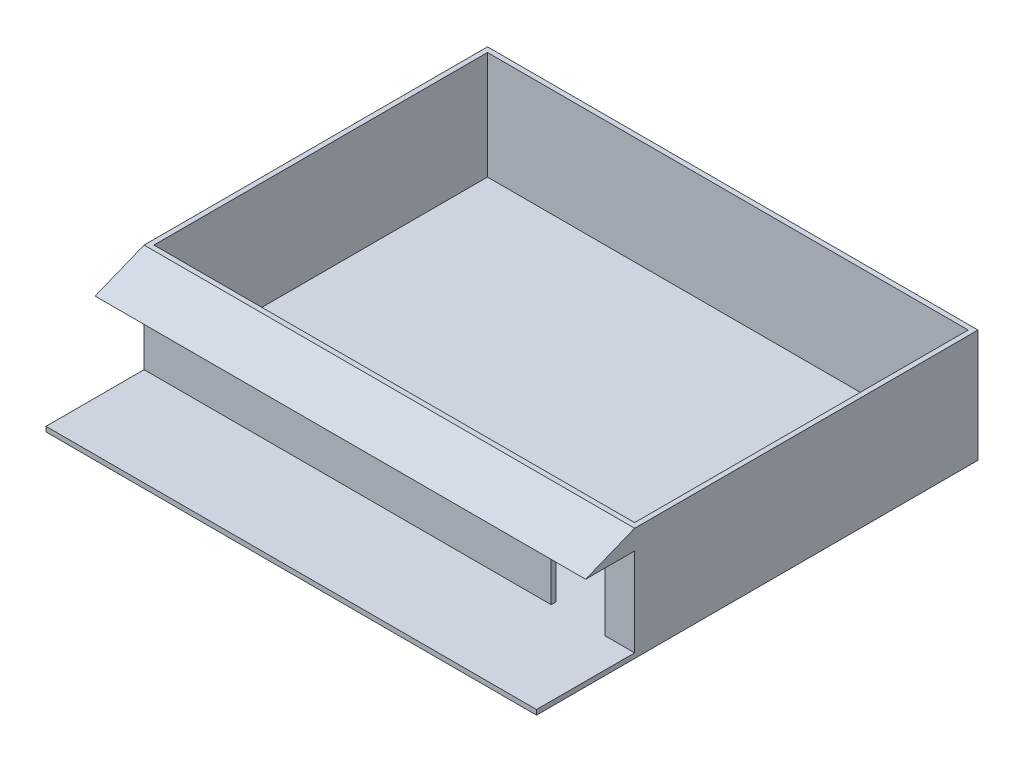
SolidWorks part; units mm, degrees
ref_plane "Front Plane" through (0, 0, 0) normal (0, 0, 1) x (1, 0, 0)
ref_plane "Top Plane" through (0, 0, 0) normal (0, 1, 0) x (1, 0, 0)
ref_plane "Right Plane" through (0, 0, 0) normal (1, 0, 0) x (0, 0, -1)
sketch "Sketch1" plane through (0, 0, 0) normal (0, 1, 0) x (1, 0, 0)
  line L1 (-500, 450) -> (500, 450)
  line L2 (-500, 450) -> (-500, -450)
  line L3 (-500, -450) -> (500, -450)
  line L4 (500, 450) -> (500, -450)
  line L5 (-500, 450) -> (500, -450) construction
  line L6 (-500, -450) -> (500, 450) construction
  point P0 (0, 0)
  dimension "D1" = 1000
  dimension "D2" = 900
extrude "Boss-Extrude1" add sketch "Sketch1" along normal blind 10
sketch "Sketch2" plane through (0, 10, 0) normal (0, 1, 0) x (1, 0, 0)
  line L1 (-500, -250) -> (500, -250)
  line L2 (-500, -250) -> (-500, 450)
  line L3 (-500, 450) -> (500, 450)
  line L4 (500, -250) -> (500, 450)
  line L5 (-500, -250) -> (500, 450) construction
  line L6 (-500, 450) -> (500, -250) construction
  line L7 (-490, -240) -> (490, -240)
  line L8 (-490, -240) -> (-490, 440)
  line L9 (-490, 440) -> (490, 440)
  line L10 (490, -240) -> (490, 440)
  line L11 (-490, -240) -> (490, 440) construction
  line L12 (-490, 440) -> (490, -240) construction
  point P0 (0, 64.0641)
  point P7 (0, 100)
  dimension "D1" = 980
  dimension "D2" = 680
  dimension "D3" = 10
extrude "Boss-Extrude2" add sketch "Sketch2" along normal blind 220
sketch "Sketch3" plane through (0, 0, 450) normal (0, 0, 1) x (1, 0, 0)
  line L0 (500, 10) -> (500, 0) construction
  line L1 (440, 180) -> (330, 180)
  line L2 (440, 180) -> (440, 10)
  line L3 (440, 10) -> (330, 10)
  line L4 (330, 180) -> (330, 10)
  line L5 (-500, 0) -> (500, 0) construction
  dimension "D1" = 60
  dimension "D2" = 170
  dimension "D3" = 10
  dimension "D4" = 110
extrude "Cut-Extrude1" cut sketch "Sketch3" against normal blind 280 contours L1 L4 L3 L2
sketch "Sketch5" plane through (-500, 0, 0) normal (-1, 0, 0) x (0, 0, 1)
  line L0 (250, 230) -> (350, 190)
  line L1 (350, 190) -> (250, 190)
  line L2 (250, 190) -> (250, 230)
  line L3 (250, 230) -> (250, 10) construction
  dimension "D1" = 100
  dimension "D2" = 40
extrude "Boss-Extrude3" add sketch "Sketch5" against normal up to surface (1000 mm away) up to face at (500, 80, 83.3333)
sketch3d "URDF Reference"
  line L0 (0, 0, 0) -> (10, 0, 0) construction
  line L1 (0, 0, 0) -> (0, 0, -10) construction
  point P0 (0, 0, 0)
  point P1 (0, 0, 0)
